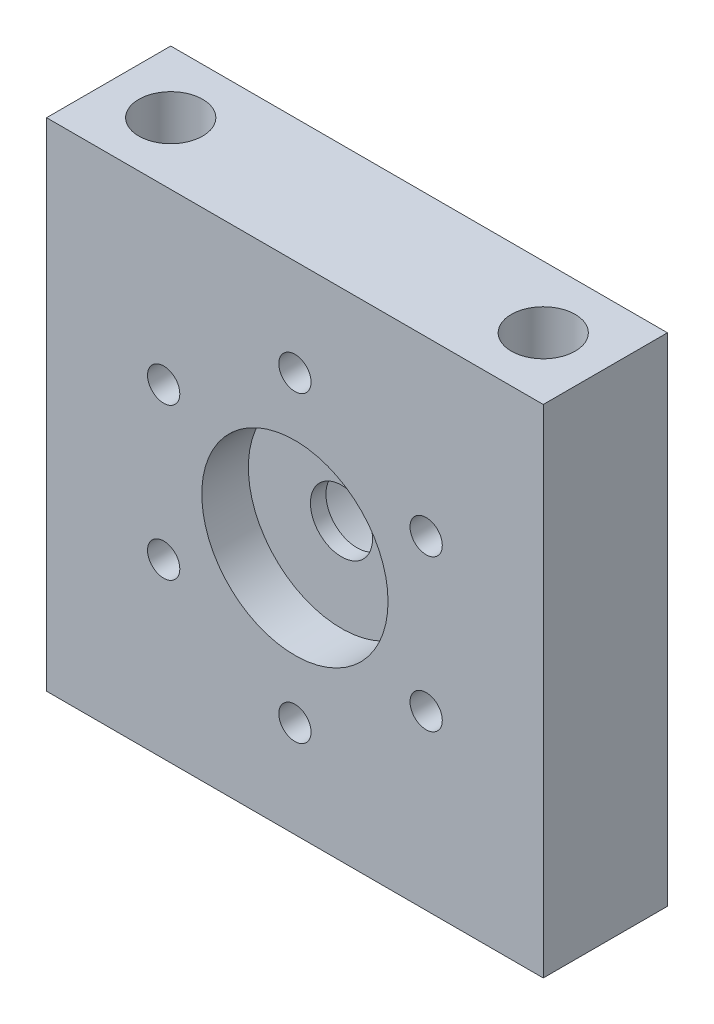
SolidWorks part; units mm, degrees
ref_plane "Front Plane" through (0, 0, 0) normal (0, 0, 1) x (1, 0, 0)
ref_plane "Top Plane" through (0, 0, 0) normal (0, 1, 0) x (1, 0, 0)
ref_plane "Right Plane" through (0, 0, 0) normal (1, 0, 0) x (0, 0, -1)
sketch "Sketch1" plane through (0, 0, 0) normal (0, 1, 0) x (1, 0, 0)
  line L1 (0, 0) -> (50.8, 0)
  line L2 (0, 0) -> (0, 12.7)
  line L3 (0, 12.7) -> (50.8, 12.7)
  line L4 (50.8, 0) -> (50.8, 12.7)
  point P9 (0, 6.35)
  point P10 (25.4, 12.7)
  point P11 (0, 0)
  point P12 (0, 0)
  dimension "D1" = 12.7
  dimension "D2" = 50.8
extrude "Boss-Extrude1" add sketch "Sketch1" along normal blind 50.8
sketch "Sketch2" plane through (0, 0, 0) normal (0, 0, 1) x (1, 0, 0)
  line L0 (0, 50.8) -> (0, 0) construction
  circle A0 centre (25.4, 25.4) radius 3.175
  point P0 (0, 25.4)
  point P8 (0, 0)
  point P9 (0, 0)
  point P10 (0, 0)
  dimension "D1" = 6.35
  dimension "D2" = 25.4
extrude "Cut-Extrude1" cut sketch "Sketch2" against normal through all
sketch "Sketch3" plane through (0, 0, 0) normal (0, 0, 1) x (1, 0, 0)
  circle A0 centre (25.4, 25.4) radius 9.525
  dimension "D1" = 19.05
extrude "Cut-Extrude2" cut sketch "Sketch3" against normal blind 4.7625
sketch "Sketch4" plane through (0, 50.8, 0) normal (0, 1, 0) x (1, 0, 0)
  line L0 (0, 12.7) -> (0, 0) construction
  line L1 (50.8, 12.7) -> (0, 12.7) construction
  circle A0 centre (6.35, 6.35) radius 3.2639
  circle A1 centre (44.45, 6.35) radius 3.2639
  point P4 (6.2864, 6.35)
  point P5 (0, 6.35)
  point P6 (25.4, 12.7)
  dimension "D1" = 6.5278
  dimension "D2" = 38.1
  dimension "D3" = 19.05
extrude "Cut-Extrude3" cut sketch "Sketch4" against normal blind 12.7
ref_plane "Plane1" through (0, 25.4, 0) normal (0, 1, 0) x (1, 0, 0)
mirror "Mirror1" about plane through (0, 25.4, 0) normal (0, 1, 0) of "Cut-Extrude3"
sketch "Sketch5" plane through (0, 0, 0) normal (0, 0, 1) x (1, 0, 0)
  circle A0 centre (25.4, 40.9) radius 1.65
  circle A4 centre (38.8234, 33.15) radius 1.65
  circle A5 centre (38.8234, 17.65) radius 1.65
  circle A6 centre (25.4, 9.9) radius 1.65
  circle A7 centre (11.9766, 17.65) radius 1.65
  circle A8 centre (11.9766, 33.15) radius 1.65
  point P15 (25.4, 25.4)
  dimension "D2" = 3.3
  dimension "D1" = 6
extrude "Cut-Extrude4" cut sketch "Sketch5" against normal through all
sketch "Sketch6" plane through (0, 0, -12.7) normal (0, 0, -1) x (-1, 0, 0)
  circle A0 centre (-25.4, 25.4) radius 7.62
  dimension "D1" = 15.24
extrude "Cut-Extrude5" cut sketch "Sketch6" against normal blind 6.35
